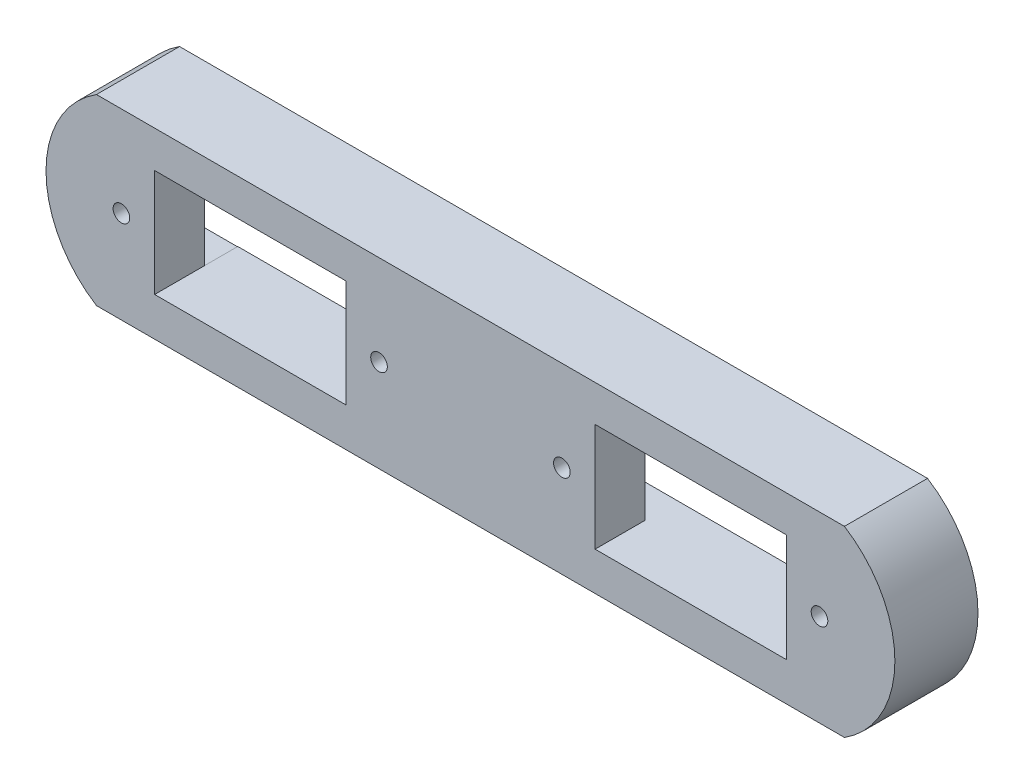
SolidWorks part; units mm, degrees
ref_plane "前视基准面" through (0, 0, 0) normal (0, 0, 1) x (1, 0, 0)
ref_plane "上视基准面" through (0, 0, 0) normal (0, 1, 0) x (1, 0, 0)
ref_plane "右视基准面" through (0, 0, 0) normal (1, 0, 0) x (0, 0, -1)
sketch "草图1" plane through (0, 0, 0) normal (0, 0, 1) x (1, 0, 0)
  line L0 (0, 6.5) -> (-20, 6.5) construction
  line L1 (0, 0) -> (33, 0)
  line L2 (0, 0) -> (0, 13)
  line L3 (0, 13) -> (33, 13)
  line L4 (33, 0) -> (33, 13)
  line L5 (-10, 6.5) -> (-10, -4.6219) construction
  line L10 (-55, 17.3781) -> (35, 17.3781)
  line L11 (-55, 17.3781) -> (-55, -4.6219)
  line L12 (-55, -4.6219) -> (35, -4.6219)
  line L13 (35, 17.3781) -> (35, -4.6219)
  line L15 (16.5, 0) -> (16.5, 13) construction
  line L16 (-48, 0.0411) -> (-48, 12.9589)
  line L22 (-25, 0.0411) -> (-25, 12.9589)
  line L23 (5, 0.0411) -> (5, 12.9589)
  line L25 (28, 0.0411) -> (28, 12.9589)
  line L29 (-20, 13) -> (-53, 13)
  line L30 (-53, 0) -> (-53, 13)
  line L31 (-20, 0) -> (-53, 0)
  line L32 (-20, 0) -> (-20, 13)
  arc A0 (-55, 17.3781) -> (-55, -4.6219) centre (-48.0718, 6.3781) ccw
  arc A1 (35, 17.3781) -> (35, -4.6219) centre (28.0718, 6.3781) cw
  point P25 (0, 0)
  dimension "D8" = 13
  dimension "D1" = 33
  dimension "D2" = 13
  dimension "D3" = 90
  dimension "D4" = 22
  dimension "D5" = 11.5
  dimension "D6" = 11.5
  dimension "D7" = 10
extrude "凸台-拉伸2" add sketch "草图1" along normal blind 10
ref_plane "基准面1" through (0, 0, 0) normal (0, 0, -1) x (-1, 0, 0)
sketch "草图2" plane through (0, 0, 0) normal (0, 0, -1) x (-1, 0, 0)
  line L1 (-33, 13) -> (-28, 13)
  line L2 (-33, 13) -> (-33, 0.0411)
  line L3 (-33, 0.0411) -> (-28, 0.0411)
  line L4 (-28, 13) -> (-28, 0.0411)
  line L5 (-5, 12.9589) -> (0, 12.9589)
  line L6 (-5, 12.9589) -> (-5, 0)
  line L7 (-5, 0) -> (0, 0)
  line L8 (0, 12.9589) -> (0, 0)
  line L9 (20, 13) -> (25, 13)
  line L10 (20, 13) -> (20, 0.0411)
  line L11 (20, 0.0411) -> (25, 0.0411)
  line L12 (25, 13) -> (25, 0.0411)
  line L13 (48, 12.9589) -> (53, 12.9589)
  line L14 (48, 12.9589) -> (48, 0)
  line L15 (48, 0) -> (53, 0)
  line L16 (53, 12.9589) -> (53, 0)
extrude "切除-拉伸2" cut sketch "草图2" against normal blind 4 contours L2 L1 L4 L3 | L6 L5 L8 L7 | L10 L9 L12 L11 | L14 L13 L16 L15
sketch "草图3" plane through (0, 0, 0) normal (0, 0, -1) x (-1, 0, 0)
  line L1 (-28, 13) -> (-5, 13)
  line L2 (-28, 13) -> (-28, 0)
  line L3 (-28, 0) -> (-5, 0)
  line L4 (-5, 13) -> (-5, 0)
  line L5 (25, 12.9589) -> (48, 12.9589)
  line L6 (25, 12.9589) -> (25, 0.0411)
  line L7 (25, 0.0411) -> (48, 0.0411)
  line L8 (48, 12.9589) -> (48, 0.0411)
extrude "切除-拉伸4" cut sketch "草图3" against normal through all contours L2 L1 L4 L3 | L6 L5 L8 L7
sketch "草图4" plane through (0, 0, 0) normal (0, 0, -1) x (-1, 0, 0)
  line L0 (-33, 13) -> (-33, 0)
  line L1 (-33, 6.5) -> (-32, 6.5)
  line L2 (-16.5, 0) -> (-16.5, 13) construction
  line L3 (10, -4.6219) -> (10, 6.5) construction
  circle A0 centre (-32, 6.5) radius 1
  circle A1 centre (-1, 6.5) radius 1
  circle A2 centre (21, 6.5) radius 1
  circle A3 centre (52, 6.5) radius 1
  dimension "D1" = 2
extrude "切除-拉伸5" cut sketch "草图4" against normal through all contours A0 | A1 | A2 | A3
